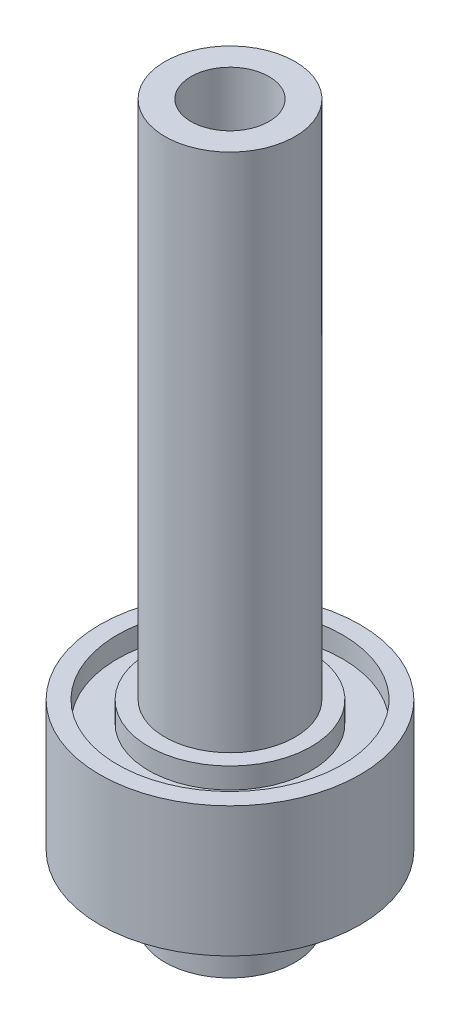
SolidWorks part; units mm, degrees
ref_plane "Front Plane" through (0, 0, 0) normal (0, 0, 1) x (1, 0, 0)
ref_plane "Top Plane" through (0, 0, 0) normal (0, 1, 0) x (1, 0, 0)
ref_plane "Right Plane" through (0, 0, 0) normal (1, 0, 0) x (0, 0, -1)
sketch "Sketch1" plane through (0, 0, 0) normal (0, 0, 1) x (1, 0, 0)
  line L0 (-3.81, 0) -> (-6.35, 0)
  line L1 (-6.35, 0) -> (-6.35, 6.35)
  line L2 (-10.9855, 6.35) -> (-12.7, 6.35)
  line L3 (-12.7, 6.35) -> (-12.7, 19.05)
  line L4 (-12.7, 19.05) -> (-10.9855, 19.05)
  line L5 (-10.9855, 19.05) -> (-10.9855, 17.018)
  line L6 (-10.9855, 17.018) -> (-7.9375, 17.018)
  line L7 (-7.9375, 17.018) -> (-7.9375, 19.05)
  line L8 (-7.9375, 19.05) -> (-6.35, 19.05)
  line L9 (-6.35, 19.05) -> (-6.35, 69.85)
  line L10 (-6.35, 69.85) -> (-3.81, 69.85)
  line L13 (-3.81, 69.85) -> (-3.81, 0)
  line L14 (0, 0) -> (0, 38.457) construction
  line L15 (-6.35, 6.35) -> (-7.9375, 6.35)
  line L16 (-7.9375, 6.35) -> (-7.9375, 8.382)
  line L17 (-7.9375, 8.382) -> (-10.9855, 8.382)
  line L18 (-10.9855, 8.382) -> (-10.9855, 6.35)
  dimension "D1" = 3.81
  dimension "D2" = 6.35
  dimension "D3" = 3.048
  dimension "D4" = 2.032
  dimension "D5" = 1.5875
  dimension "D6" = 12.7
  dimension "D7" = 1.5875
  dimension "D8" = 50.8
  dimension "D9" = 3.048
  dimension "D10" = 6.35
  dimension "D11" = 12.7
  dimension "D12" = 2.032
revolve "Revolve1" add sketch "Sketch1" angle 360 about L14
